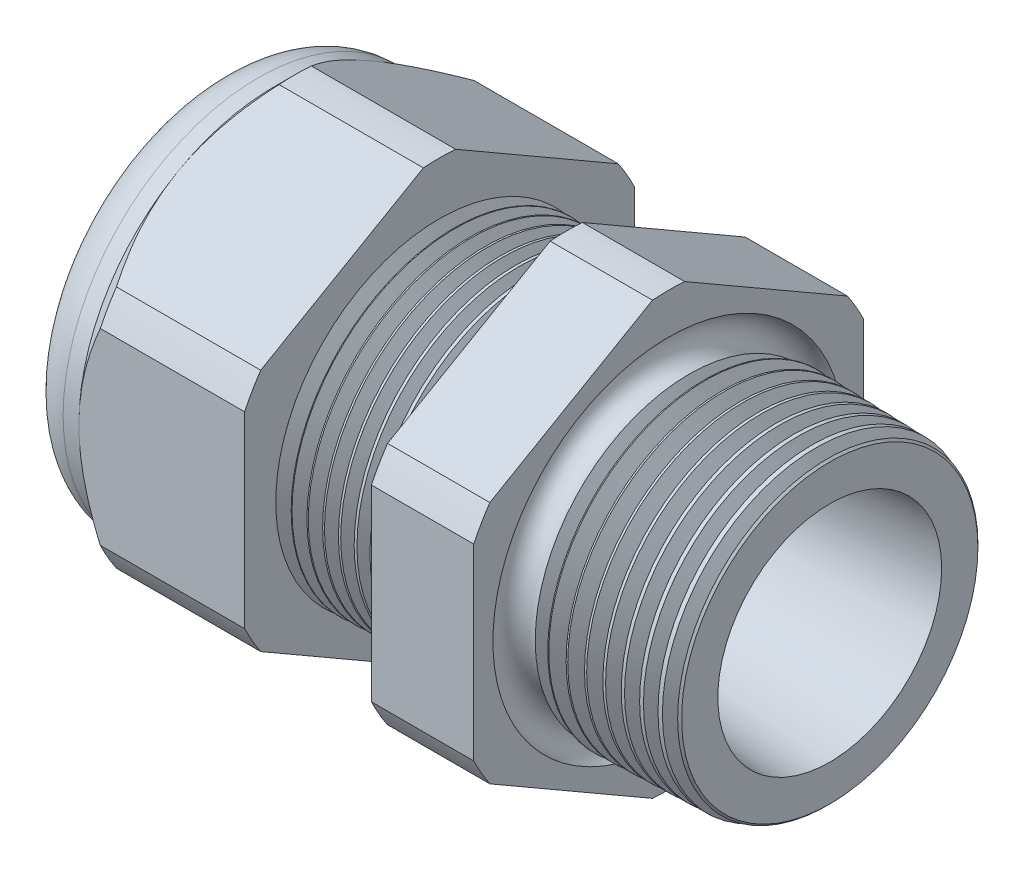
SolidWorks part; units mm, degrees
ref_plane "Front Plane" through (0, 0, 0) normal (0, 0, 1) x (1, 0, 0)
ref_plane "Top Plane" through (0, 0, 0) normal (0, 1, 0) x (1, 0, 0)
ref_plane "Right Plane" through (0, 0, 0) normal (1, 0, 0) x (0, 0, -1)
sketch "Sketch10" plane through (0, 0, 0) normal (0, 0, 1) x (1, 0, 0)
  line L0 (0, 0) -> (-115.3565, 0) construction
  line L1 (-29.972, 3.937) -> (-19.072, 3.937)
  line L2 (0, 5.4696) -> (0, 7.5016)
  line L3 (-7.874, 7.7078) -> (0, 7.5016)
  line L4 (-7.874, 19.05) -> (-7.874, 7.7078)
  line L5 (-7.874, 19.05) -> (-12.874, 19.05)
  line L6 (-12.874, 19.05) -> (-12.874, 7.8387)
  line L7 (-19.072, 8.001) -> (-12.874, 7.8387)
  line L8 (-19.072, 8.001) -> (-19.072, 19.05)
  line L9 (-19.072, 19.05) -> (-27.172, 19.05)
  line L10 (-27.172, 19.05) -> (-27.172, 9.525)
  line L11 (-27.172, 9.525) -> (-29.972, 9.525)
  line L12 (-29.972, 9.525) -> (-29.972, 3.937)
  line L13 (-19.072, 3.937) -> (0, 5.4696)
  dimension "D1" = 29.972
  dimension "D2" = 7.874
  dimension "D3" = 1.5
  dimension "D4" = 2.032
  dimension "A" = 16.002
  dimension "D6" = 19.05
  dimension "D8" = 38.1
  dimension "D9" = 2.8
  dimension "D10" = 8.1
  dimension "D11" = 5
  dimension "D" = 7.874
revolve "Revolve2" add sketch "Sketch10" angle 360 about L0
sketch "Sketch12" plane through (-27.172, 0, 0) normal (-1, 0, 0) x (0, 0, 1)
  line L1 (-0.7885, 10.5433) -> (-8.7365, 5.9545)
  line L2 (-9.525, 4.5888) -> (-9.525, -4.5888)
  line L3 (-8.7365, -5.9545) -> (-0.7885, -10.5433)
  line L4 (0.7885, -10.5433) -> (8.7365, -5.9545)
  line L5 (9.525, -4.5888) -> (9.525, 4.5888)
  line L6 (8.7365, 5.9545) -> (0.7885, 10.5433)
  circle A0 centre (0, 0) radius 9.525 construction
  arc A1 (0.7885, 10.5433) -> (-0.7885, 10.5433) centre (0, 0) ccw
  arc A2 (-8.7365, 5.9545) -> (-9.525, 4.5888) centre (0, 0) ccw
  arc A3 (-9.525, -4.5888) -> (-8.7365, -5.9545) centre (0, 0) ccw
  arc A4 (-0.7885, -10.5433) -> (0.7885, -10.5433) centre (0, 0) ccw
  arc A5 (8.7365, -5.9545) -> (9.525, -4.5888) centre (0, 0) ccw
  arc A6 (9.525, 4.5888) -> (8.7365, 5.9545) centre (0, 0) ccw
  dimension "D2" = 21.1455
  dimension "D1" = 19.05
extrude "Cut-Extrude2" cut sketch "Sketch12" against normal through all flip side to cut
fillet "Fillet4" radius 2.032 1 edges at (-29.972, 0, -9.525)
sketch "Sketch19" plane through (-27.172, 0, 0) normal (-1, 0, 0) x (0, 0, 1)
  line L0 (9.525, 0) -> (9.525, 4.5888) construction
  circle A0 centre (0, 0) radius 9.525
extrude "Cut-Extrude3" cut sketch "Sketch19" against normal blind 2 draft 45 flip side to cut
chamfer "Chamfer1" distance 0.254 angle 45 1 edges at (0, 0, -7.5016)
sketch "Sketch21" plane through (-29.972, 0, 0) normal (-1, 0, 0) x (0, 0, 1)
  circle A0 centre (0, 0) radius 3.937
  circle A2 centre (0, 0) radius 3.937 construction
extrude "plug" add sketch "Sketch21" against normal blind 3.81 separate body
sketch "Sketch22" plane through (-29.972, 0, 0) normal (-1, 0, 0) x (0, 0, 1)
  circle A0 centre (0, 0) radius 3.683
  circle A1 centre (0, 0) radius 3.937 construction
  dimension "D1" = 0.254
extrude "Cut-Extrude4" cut sketch "Sketch22" against normal blind 0.508
sketch "Sketch27" plane through (-29.464, 0, 0) normal (-1, 0, 0) x (0, 0, 1)
  line L0 (-4.3624, 0) -> (4.3624, 0) construction
  circle A0 centre (-2.5354, 0) radius 1.143
  circle A1 centre (0, 0) radius 3.683 construction
  dimension "D1" = 0.0046
  dimension "holedia" = 2.286
extrude "plugholes" cut sketch "Sketch27" against normal through all
pattern_circular "CirPattern1" count 4 over 360 about axis through (0, 0, 0) along (1, 0, 0) of "plugholes"
sketch "Sketch28" [suppressed] plane through (-29.464, 0, 0) normal (-1, 0, 0) x (0, 0, 1)
  circle A0 centre (0, 0) radius 0.762
  dimension "midholedia" = 2.286
extrude "midhole" [suppressed] cut sketch "Sketch28" against normal through all
sketch "Sketch29" plane through (0, 0, 0) normal (0, 0, 1) x (1, 0, 0)
  line L0 (-19.072, 8.001) -> (-18.339, 7.9818)
  line L1 (-12.874, 7.8387) -> (-19.072, 8.001) construction
  line L2 (-18.339, 7.9818) -> (-18.7221, 7.3566)
  line L3 (-18.7221, 7.3566) -> (-19.072, 8.001)
  dimension "D1" = 60
  dimension "D2" = 60
  dimension "D3" = 0.635
revolve "Cut-Revolve1" cut sketch "Sketch29" angle 360 about axis through (0, 0, 0) along (-1, 0, 0)
pattern_linear "LPattern1" count 8 spacing 0.762 along (1, 0, 0) of "Cut-Revolve1"
sketch "Sketch30" plane through (0, 0, 0) normal (0, 0, 1) x (1, 0, 0)
  line L0 (-7.874, 7.7078) -> (-6.9944, 7.6847)
  line L1 (-7.874, 10.5433) -> (-7.874, 5.9545) construction
  line L2 (-0.2539, 7.5082) -> (-7.874, 7.7078) construction
  line L3 (-6.9944, 7.6847) -> (-7.4542, 6.9345)
  line L4 (-7.4542, 6.9345) -> (-7.874, 7.7078)
  dimension "D1" = 60
  dimension "D2" = 60
  dimension "D3" = 0.762
revolve "Cut-Revolve2" cut sketch "Sketch30" angle 360 about axis through (0, 0, 0) along (-1, 0, 0)
pattern_linear "LPattern2" count 9 spacing 0.889 along (1, 0, 0) of "Cut-Revolve2"
sketch "Sketch31" [suppressed] plane through (-38.354, 0, 0) normal (-1, 0, 0) x (0, 0, 1)
  line L0 (-1.905, 1.905) -> (1.905, 1.905)
  line L1 (-1.905, -1.905) -> (1.905, -1.905)
  circle A0 centre (0, 0) radius 1.905 construction
  arc A1 (-1.905, 1.905) -> (-1.905, -1.905) centre (-1.905, 0) ccw
  arc A2 (1.905, 1.905) -> (1.905, -1.905) centre (1.905, 0) cw
extrude "Cut-Extrude5" [suppressed] cut sketch "Sketch31" against normal through all
sketch "Sketch32" plane through (0, 0, 0) normal (0, 0, 1) x (1, 0, 0)
  line L0 (-7.874, 10.5433) -> (-7.874, 5.9545) construction
  circle A0 centre (-7.747, 7.7078) radius 0.889
  dimension "D2" = 1.778
  dimension "D1" = 0.127
revolve "Cut-Revolve3" cut sketch "Sketch32" angle 360 about axis through (0, 0, 0) along (-1, 0, 0)
